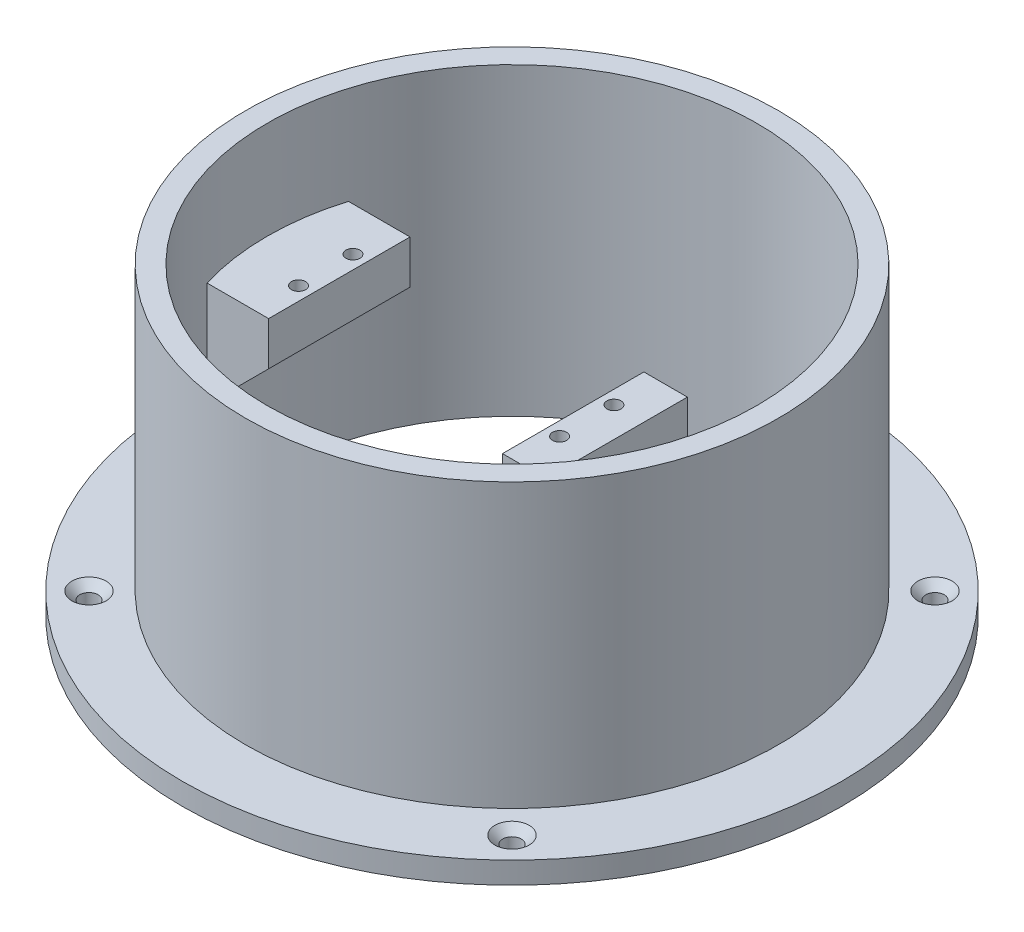
SolidWorks part; units mm, degrees
ref_plane "Front Plane" through (0, 0, 0) normal (0, 0, 1) x (1, 0, 0)
ref_plane "Top Plane" through (0, 0, 0) normal (0, 1, 0) x (1, 0, 0)
ref_plane "Right Plane" through (0, 0, 0) normal (1, 0, 0) x (0, 0, -1)
sketch "Sketch1" plane through (0, 0, 0) normal (0, 1, 0) x (1, 0, 0)
  circle A0 centre (0, 0) radius 60.625
  circle A1 centre (0, 0) radius 45
  dimension "D1" = 121.25
  dimension "D2" = 90
extrude "Boss-Extrude1" add sketch "Sketch1" along normal blind 4 contours A0
sketch "Sketch2" plane through (0, 4, 0) normal (0, 1, 0) x (1, 0, 0)
  circle A0 centre (0, 0) radius 45 construction
  circle A1 centre (0, 0) radius 45
  circle A2 centre (0, 0) radius 49
  dimension "D1" = 4
extrude "Boss-Extrude2" add sketch "Sketch2" along normal blind 52
ref_plane "Plane1" through (0, 36, 0) normal (0, 1, 0) x (1, 0, 0)
sketch "Sketch4" plane through (0, 0, 0) normal (0, 0, 1) x (1, 0, 0)
  line L0 (-60.625, 0) -> (60.625, 0) construction
  line L1 (11.25, 38) -> (19.25, 38)
  line L2 (11.25, 38) -> (11.25, 0)
  line L3 (11.25, 0) -> (19.25, 0)
  line L4 (19.25, 38) -> (19.25, 0)
  line L5 (49, 56) -> (-49, 56) construction
  line L6 (-45, 56) -> (-45, 4)
  line L7 (-31.75, 38) -> (-46.75, 38)
  line L8 (-31.75, 38) -> (-31.75, 30)
  line L9 (-31.75, 30) -> (-46.75, 30)
  line L10 (-46.75, 38) -> (-46.75, 30)
  line L11 (60.625, 4) -> (-60.625, 4) construction
  line L12 (-31.75, 30) -> (-45, 16.75)
  dimension "D1" = 11.25
  dimension "D2" = 8
  dimension "D3" = 18
  dimension "D4" = 43
  dimension "D5" = 15
  dimension "D6" = 8
  dimension "D7" = 45
  dimension "D8" = 18
extrude "Boss-Extrude4" add sketch "Sketch4" along normal mid plane 26 contours L9 L8 L7 L6 | L12 L9 L6 | L1 L4 L3 L2
sketch "Sketch5" plane through (0, 0, 0) normal (0, -1, 0) x (1, 0, 0)
  line L0 (11.25, 13) -> (29.0674, 34.3524)
  line L1 (11.25, -13) -> (29.0674, -34.3524)
  line L2 (11.25, 13) -> (11.25, -13)
  circle A0 centre (0, 0) radius 45 construction
  arc A1 (29.0674, -34.3524) -> (29.0674, 34.3524) centre (0, 0) ccw
extrude "Boss-Extrude5" add sketch "Sketch5" against normal up to surface (4 mm away) contours L0 A1 L1 L2 up to face at (0, 4, 60.625)
sketch "Sketch7" plane through (0, 38, 0) normal (0, 1, 0) x (1, 0, 0)
  line L0 (-31.75, -13) -> (-31.75, 13) construction
  circle A0 centre (-34.25, 5) radius 1.3
  circle A1 centre (-34.25, -5) radius 1.3
  circle A2 centre (13.75, 5) radius 1.3
  circle A3 centre (13.75, -5) radius 1.3
  dimension "D1" = 2.6
  dimension "D2" = 2.6
  dimension "D3" = 10
  dimension "D4" = 5
  dimension "D5" = 2.5
  dimension "D7" = 48
  dimension "D6" = 2
extrude "Cut-Extrude4" cut sketch "Sketch7" against normal through all
sketch "Sketch9" plane through (11.25, 0, 0) normal (-1, 0, 0) x (0, 0, 1)
  line L0 (13, 0) -> (-13, 0) construction
  line L1 (-5, 29) -> (5, 29)
  line L2 (-5, 29) -> (-5, 0)
  line L3 (-5, 0) -> (5, 0)
  line L4 (5, 29) -> (5, 0)
  line L5 (-5, 29) -> (5, 0) construction
  line L6 (-5, 0) -> (5, 29) construction
  line L7 (0, 0) -> (0, 29) construction
  line L8 (13, 38) -> (-13, 38) construction
  line L10 (5, 5) -> (-5, 5)
  point P0 (0, 14.5)
  dimension "D1" = 10
  dimension "D2" = 9
  dimension "D3" = 5
extrude "Cut-Extrude7" cut sketch "Sketch9" against normal up to surface (8 mm away) contours L10 L4 L1 L2 up to face at (19.25, 21, 0)
sketch "Sketch12" plane through (0, 4, 0) normal (0, 1, 0) x (1, 0, 0)
  line L5 (27.25, 19.6878) -> (27.25, -19.6878)
  line L6 (27.25, 19.6878) -> (27.25, -19.6878)
  line L9 (24.25, 16.0926) -> (24.25, -16.0926)
  line L10 (19.25, -13) -> (19.25, 13) construction
  line L18 (27.25, -19.6878) -> (29.4795, -22.3597)
  line L19 (29.4795, 22.3597) -> (27.25, 19.6878)
  line L21 (24.25, -16.0926) -> (29.4795, -22.3597)
  line L22 (29.4795, 22.3597) -> (24.25, 16.0926)
  arc A2 (29.4795, -22.3597) -> (29.4795, 22.3597) centre (0, 0) ccw
  arc A3 (29.4795, -22.3597) -> (29.4795, 22.3597) centre (0, 0) ccw
  dimension "D2" = 5
  dimension "D1" = 8
extrude "Cut-Extrude9" cut sketch "Sketch12" against normal through all contours L21 A3 L22 L6 | L6 L22 L9 L21
sketch "Sketch14" plane through (0, 4, 0) normal (0, 1, 0) x (1, 0, 0)
  line L0 (0, 0) -> (-38.8909, 38.8909) construction
  line L1 (11.25, 13) -> (19.25, 13) construction
  circle A0 centre (-38.8909, 38.8909) radius 1.5
  circle A1 centre (38.8909, 38.8909) radius 1.5
  circle A2 centre (38.8909, -38.8909) radius 1.5
  circle A3 centre (-38.8909, -38.8909) radius 1.5
  point P15 (0, 0)
  dimension "D1" = 3
  dimension "D2" = 55
  dimension "D3" = 135
  dimension "D4" = 4
hole_wizard "CSK for M3 Countersunk Flat Head Screw1" positions "Sketch15" profile "Sketch17" countersink size "M3" standard "DIN" end condition up to next
sketch "Sketch15" plane through (0, 4, 0) normal (0, 1, 0) x (1, 0, 0)
  point P0 (-38.8909, 38.8909)
  point P3 (-38.8909, -38.8909)
  point P6 (38.8909, -38.8909)
  point P9 (38.8909, 38.8909)
sketch "Sketch17" plane through (-38.8909, 4, -38.8909) normal (1, 0, 0) x (0, 0, 1)
  line L0 (0, 0) -> (0, 4)
  line L1 (0, 4) -> (1.7, 4)
  line L2 (1.7, 4) -> (1.7, 1.45)
  line L3 (1.7, 1.45) -> (3.15, 0)
  line L5 (3.15, 0) -> (0, 0)
  line L6 (-1.7, 1.45) -> (-3.15, 0) construction
  line L11 (0, -6.35) -> (0, 107.95) construction
  dimension "Thru Hole Dia." = 3.4
  dimension "Thru Hole Depth" = 4
  dimension "Near C'Sink Dia." = 6.3
  dimension "Near C'Sink Angle" = 90
